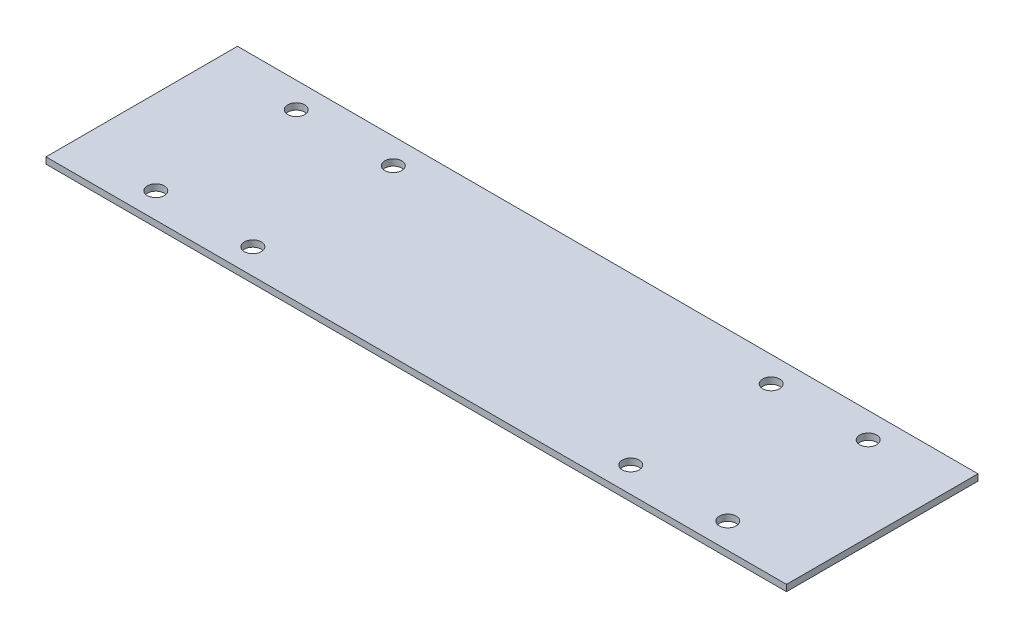
SolidWorks part; units mm, degrees
ref_plane "Front Plane" through (0, 0, 0) normal (0, 0, 1) x (1, 0, 0)
ref_plane "Top Plane" through (0, 0, 0) normal (0, 1, 0) x (1, 0, 0)
ref_plane "Right Plane" through (0, 0, 0) normal (1, 0, 0) x (0, 0, -1)
sketch "Sketch1" plane through (0, 0, 0) normal (0, 1, 0) x (1, 0, 0)
  line L1 (-71.5585, 30.0748) -> (73.4415, 30.0748)
  line L2 (-71.5585, 30.0748) -> (-71.5585, -7.4252)
  line L3 (-71.5585, -7.4252) -> (73.4415, -7.4252)
  line L4 (73.4415, 30.0748) -> (73.4415, -7.4252)
  circle A0 centre (-55.0585, 25.0748) radius 1.66
  circle A1 centre (-36.0585, 25.0748) radius 1.66
  circle A2 centre (-55.0585, -2.4252) radius 1.66
  circle A3 centre (-36.0585, -2.4252) radius 1.66
  circle A4 centre (37.9415, 25.0748) radius 1.66
  circle A5 centre (56.9415, 25.0748) radius 1.66
  circle A6 centre (37.9415, -2.4252) radius 1.66
  circle A7 centre (56.9415, -2.4252) radius 1.66
  point P20 (0, 0)
  point P21 (0, 0)
  point P22 (0, 0)
  point P23 (0, 0)
  point P24 (0, 0)
  dimension "D3" = 3.32
  dimension "D1" = 145
  dimension "D2" = 37.5
  dimension "D4" = 16.5
  dimension "D5" = 16.5
  dimension "D6" = 19
  dimension "D7" = 19
  dimension "D8" = 27.5
  dimension "D9" = 5
  dimension "D10" = 5
  dimension "D11" = 27.5
extrude "Boss-Extrude1" add sketch "Sketch1" along normal blind 1.25
